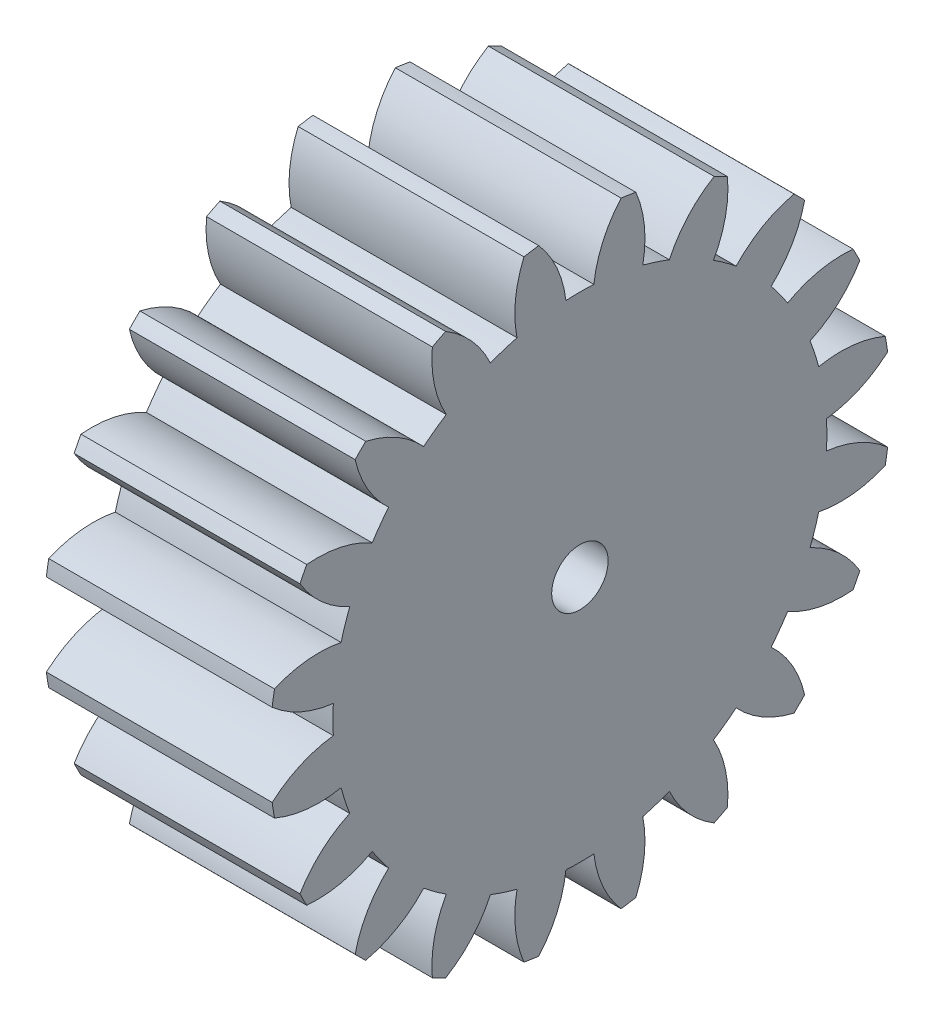
SolidWorks part; units mm, degrees
ref_plane "Plane1" through (0, 0, 0) normal (0, 0, 1) x (1, 0, 0)
ref_plane "Plane2" through (0, 0, 0) normal (0, 1, 0) x (1, 0, 0)
ref_plane "Plane3" through (0, 0, 0) normal (1, 0, 0) x (0, 0, -1)
sketch "HoldingSke" plane through (0, 0, 0) normal (0, 1, 0) x (1, 0, 0)
  line L0 (0, 0) -> (0.3759, -0.1368)
  line L1 (-15, 0) -> (100, 0) construction
  line L2 (0, 0) -> (-2.1039, 2.3779)
  line L3 (0, 0) -> (-11.863, 4.5341)
  line L4 (0, 0) -> (8.1152, 2.9537)
  line L5 (0, 0) -> (-46.8476, -17.4728)
  line L6 (0, 0) -> (-16.5793, -11.1861)
  line L7 (-2.1039, 2.3779) -> (8.6586, 51.2059)
  line L8 (-76.2, 54.61) -> (-75.3, 54.61)
  line L9 (-71.009, 38.7566) -> (-53.1078, 45.2721)
  line L10 (-76.2, 71.12) -> (104.1128, 71.12)
  line L11 (0, 0) -> (-20, 0)
  line L12 (-76.2, 101.6) -> (-76.113, 101.6)
  line L13 (24.9733, 27.94) -> (52.9518, 28.4284)
  line L14 (24.9733, 27.94) -> (24.9743, 27.94)
  line L15 (24.9733, 27.94) -> (100.4006, 29.5858)
  line L16 (-63.627, -2.5) -> (-12.827, -2.5)
  circle A0 centre (0, 0) radius 2.5
  circle A1 centre (0, 0) radius 21.874
  circle A2 centre (0, 0) radius 37.5
  circle A3 centre (0, 0) radius 2.5
  dimension "MHD" = 43.748
  dimension "Hub_dia" = 75
  dimension "Bore" = 5
  dimension "MBD" = 5
  dimension "Num_teeth" = 20
  dimension "Pitch" = 0.4
  dimension "Overall_len" = 50
  dimension "Show_teeth" = 20
  dimension "Thickness" = 20
  dimension "OAL" = 50.0001
  dimension "T_dim" = 0.9
  dimension "Ap" = 20
  dimension "H" = 19.05
  dimension "Pitch_radius" = 180.3128
  dimension "Width" = 20
  dimension "Backlash" = 0.087
  dimension "Addendum_fac" = 1
  dimension "Dedendum_fac" = 1.25
  dimension "Clearance_fac" = 0.25
  dimension "Dedendum_add" = 0.001
  dimension "Module" = 2.5
sketch "BasProSke" plane through (0, 0, 0) normal (0, 1, 0) x (1, 0, 0)
  line L0 (-10, 0) -> (60, 0) construction
  line L1 (0, 0) -> (0, 27.5)
  line L2 (0, 0) -> (20, 0)
  line L3 (20, 0) -> (20, 27.5)
  line L4 (20, 27.5) -> (0, 27.5)
  dimension "Thickness" = 20
  dimension "Diameter" = 55
revolve "Base-Revolve" add sketch "BasProSke" angle 360 about L0
sketch "TooCutSke" plane through (0, 0, 0) normal (1, 0, 0) x (0, 0, -1)
  line L1 (0, 0) -> (0, 107) construction
  line L2 (0, 0) -> (-2.1137, 24.9105) construction
  line L3 (0, 0) -> (-7.8012, 49.2549) construction
  line L4 (-2.1137, 24.9105) -> (-3.9006, 24.6275) construction
  arc A0 (1.2377, 21.839) -> (-1.2377, 21.839) centre (0, 0) ccw
  arc A1 (3.6672, 27.28) -> (-3.6672, 27.28) centre (0, 0) ccw
  circle A2 centre (0, 0) radius 25 construction
  circle A3 centre (0, 0) radius 23.4923 construction
  arc A4 (-1.2377, 21.839) -> (-3.6672, 27.28) centre (-11.1689, 20.6675) ccw
  arc A5 (3.6672, 27.28) -> (1.2377, 21.839) centre (11.1689, 20.6675) ccw
  dimension "Root_dia" = 43.748
  dimension "Overcut_dia" = 55.0508
  dimension "Pitch_dia" = 50
  dimension "Base_dia" = 46.9846
  dimension "Flank_rad" = 10
  dimension "Half_ang" = 9
  dimension "Half_CT" = 1.8092
extrude "ToothCut" cut sketch "TooCutSke" along normal through all
fillet "Breaks" [suppressed] radius 0.05
fillet "RootFillets" [suppressed] radius 0.626
pattern_circular "TeethCuts" count 20 every 18 about axis through (-10, 0, 0) along (1, 0, 0) of "ToothCut", "RootFillets", "Breaks"
sketch "HubNeaOneSke" plane through (0, 0, 0) normal (-1, 0, 0) x (0, 0, 1)
  circle A0 centre (0, 0) radius 21.874
  dimension "Diameter" = 43.748
extrude "HubNearOne" [suppressed] add sketch "HubNeaOneSke" along normal blind 30.0001
sketch "HubNeaBotSke" plane through (0, 0, 0) normal (-1, 0, 0) x (0, 0, 1)
  circle A0 centre (0, 0) radius 21.874
  dimension "Diameter" = 43.748
extrude "HubNearBoth" [suppressed] add sketch "HubNeaBotSke" along normal blind 15
ref_plane "FarPln" through (20, 0, 0) normal (1, 0, 0) x (0, 0, -1)
sketch "HubFarSke" plane through (20, 0, 0) normal (1, 0, 0) x (0, 0, -1)
  circle A0 centre (0, 0) radius 21.874
  dimension "Diameter" = 43.748
extrude "HubFar" [suppressed] add sketch "HubFarSke" along normal blind 15
sketch "BorSke" plane through (0, 0, 0) normal (1, 0, 0) x (0, 0, -1)
  circle A0 centre (0, 0) radius 2.5
  dimension "Diameter" = 5
extrude "Bore" cut sketch "BorSke" along normal mid plane 100.0001
sketch "KeySke" plane through (0, 0, 0) normal (1, 0, 0) x (0, 0, -1)
  line L0 (-1, 0) -> (-1, 3.4)
  line L1 (-1, 3.4) -> (1, 3.4)
  line L2 (1, 3.4) -> (1, 0)
  line L3 (0, 0) -> (0, 34) construction
  line L4 (-1, 0) -> (1, 0)
  dimension "Offset" = 3.4
extrude "Keyway" [suppressed] cut sketch "KeySke" along normal mid plane 100.0001
pattern_circular "Keyway2" [suppressed] count 2 every 90 about axis through (-10, 0, 0) along (1, 0, 0)
equation "' \"Module@HoldingSke\" = 6.35"
equation "' \"Num_teeth@HoldingSke\" = 12"
equation "' \"Ap@HoldingSke\" =  20"
equation "' \"Ap@HoldingSke\" = 20"
equation "' \"Width@HoldingSke\" = 0.5 * 25.4"
equation "' \"Hub_dia@HoldingSke\"= 1 * 25.4"
equation "' \"Hub_dia@HoldingSke\" = 1 * 25.4"
equation "' \"Overall_len@HoldingSke\" = 1.0 * 25.4"
equation "' \"Bore@HoldingSke\" = 0.75 * 25.4"
equation "' \"T_dim@HoldingSke\" = 0.1 * 25.4"
equation "' \"Width@KeySke\" = 0.25 * 25.4"
equation "' \"Show_teeth@HoldingSke\" = 13"
equation "' \"Backlash@HoldingSke\" = 0.009 * 25.4"
equation "' \"Addendum_fac@HoldingSke\" = 1.0"
equation "' \"Dedendum_fac@HoldingSke\" = 1.25"
equation "' \"Dedendum_add@HoldingSke\" = 0.00005 * 25.4"
equation "' \"Clearance_fac@HoldingSke\" = 0.25"
equation "\"Pitch@HoldingSke\" = 1 / \"Module@HoldingSke\""
equation "\"Overcut_dia@TooCutSke\" = (\"Num_teeth@HoldingSke\" + 2 * \"Addendum_fac@HoldingSke\") / \"Pitch@HoldingSke\" + 0.002 * 25.4"
equation "\"Pitch_dia@TooCutSke\" = \"Num_teeth@HoldingSke\" / \"Pitch@HoldingSke\""
equation "\"Base_dia@TooCutSke\" = \"Num_teeth@HoldingSke\" / \"Pitch@HoldingSke\" * cos((\"Ap@HoldingSke\"  * 3.14159265 / 180))"
equation "\"Root_dia@TooCutSke\" = (\"Num_teeth@HoldingSke\" + 2) / \"Pitch@HoldingSke\" - 2 * (\"Addendum_fac@HoldingSke\" + \"Dedendum_fac@HoldingSke\") / \"Pitch@HoldingSke\" - \"Dedendum_add@HoldingSke\" * 2"
equation "\"Half_ang@TooCutSke\" = 180 / \"Num_teeth@HoldingSke\""
equation "\"Half_CT@TooCutSke\" = \"Num_teeth@HoldingSke\" / \"Pitch@HoldingSke\" * sin((3.14159265 / 2 / \"Num_teeth@HoldingSke\")) / 2 - 7 * \"Backlash@HoldingSke\" / 4"
equation "\"Flank_rad@TooCutSke\" = \"Num_teeth@HoldingSke\" / \"Pitch@HoldingSke\" / 5"
equation "\"Radius@RootFillets\" = \"Clearance_fac@HoldingSke\" / \"Pitch@HoldingSke\" + \"Dedendum_add@HoldingSke\""
equation "\"Break_rad@Breaks\" = 0.02 / \"Pitch@HoldingSke\""
equation "\"Thickness@HoldingSke\" = \"Width@HoldingSke\""
equation "\"OAL@HoldingSke\" = \"Thickness@HoldingSke\""
equation "\"MHD@HoldingSke\" = (\"Num_teeth@HoldingSke\" + 2) / \"Pitch@HoldingSke\" - 2 * (\"Addendum_fac@HoldingSke\" + \"Dedendum_fac@HoldingSke\")  / \"Pitch@HoldingSke\" - \"Dedendum_add@HoldingSke\" * 2"
equation "\"MBD@HoldingSke\" = (\"Num_teeth@HoldingSke\" + 2) / \"Pitch@HoldingSke\" - 2 * (\"Addendum_fac@HoldingSke\" + \"Dedendum_fac@HoldingSke\")  / \"Pitch@HoldingSke\" - \"Dedendum_add@HoldingSke\" * 2 - 0.002 * 25.4"
equation "\"MHD@HoldingSke\" = ((sgn( \"MHD@HoldingSke\" - \"Hub_dia@HoldingSke\" )-1)*( \"MHD@HoldingSke\" - \"Hub_dia@HoldingSke\" ))/-2+ \"Hub_dia@HoldingSke\""
equation "\"MBD@HoldingSke\" = ((sgn( \"MBD@HoldingSke\" - \"Bore@HoldingSke\" )-1)*( \"MBD@HoldingSke\" - \"Bore@HoldingSke\" ))/-2+ \"Bore@HoldingSke\""
equation "\"OAL@HoldingSke\" = ((sgn( \"OAL@HoldingSke\" - \"Overall_len@HoldingSke\" )+1)*( \"OAL@HoldingSke\" - \"Overall_len@HoldingSke\" ))/2 + \"Overall_len@HoldingSke\" + 0.000002 * 25.4"
equation "\"Num_teeth@TeethCuts\" = int( \"Show_teeth@HoldingSke\" ) + 1"
equation "\"Num_teeth@TeethCuts\" = ((sgn( \"Num_teeth@TeethCuts\" - \"Num_teeth@HoldingSke\" )-1)*( \"Num_teeth@TeethCuts\" - \"Num_teeth@HoldingSke\" ))/-2+ \"Num_teeth@HoldingSke\""
equation "\"Num_teeth@TeethCuts\" = ((sgn( \"Num_teeth@TeethCuts\" - 2.0)+1)*( \"Num_teeth@TeethCuts\" - 2.0))/2 +2.0"
equation "\"Angle@TeethCuts\" = 360.0 / \"Num_teeth@HoldingSke\""
equation "\"Diameter@BasProSke\" = (\"Num_teeth@HoldingSke\" + 2 * \"Addendum_fac@HoldingSke\") / \"Pitch@HoldingSke\""
equation "\"Thickness@BasProSke\"  = \"Thickness@HoldingSke\""
equation "' \"Fillet_rad@BasProSke\" =  \"Thickness@HoldingSke\" * 0.05"
equation "' \"Fillet_rad@BasProSke\" = \"Thickness@HoldingSke\" * 0.05"
equation "\"MHD@HoldingSke\" = ((sgn( \"MHD@HoldingSke\" - \"Root_dia@TooCutSke\" )-1)*( \"MHD@HoldingSke\" - \"Root_dia@TooCutSke\" ))/-2+ \"Root_dia@TooCutSke\""
equation "\"Diameter@HubNeaOneSke\" = \"MHD@HoldingSke\""
equation "\"Length@HubNearOne\" = \"OAL@HoldingSke\" - \"Thickness@BasProSke\""
equation "\"Diameter@HubNeaBotSke\" = \"MHD@HoldingSke\""
equation "\"Length@HubNearBoth\" = ( \"OAL@HoldingSke\" - \"Thickness@BasProSke\" ) / 2.0"
equation "\"Thickness@FarPln\" = \"Thickness@BasProSke\""
equation "\"Diameter@HubFarSke\" = \"MHD@HoldingSke\""
equation "\"Length@HubFar\" = ( \"OAL@HoldingSke\" - \"Thickness@BasProSke\" ) / 2.0"
equation "\"Diameter@BorSke\" = \"MBD@HoldingSke\""
equation "\"D1@Bore\" = \"OAL@HoldingSke\" * 2.0"
equation "\"D1@Keyway\" = \"OAL@HoldingSke\" * 2.0"
equation "\"Offset@KeySke\" = \"T_dim@HoldingSke\" + \"MBD@HoldingSke\" / 2.0"
